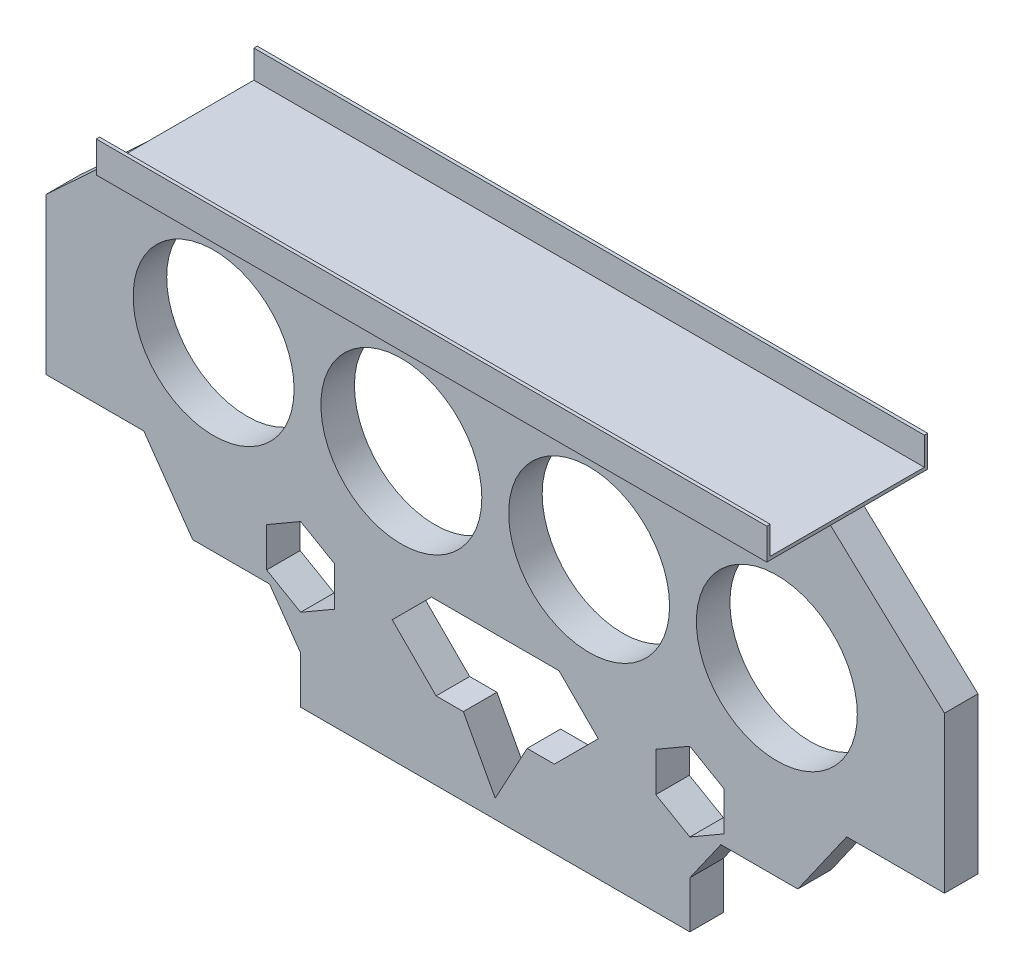
SolidWorks part; units mm, degrees
ref_plane "Front Plane" through (0, 0, 0) normal (0, 0, 1) x (1, 0, 0)
ref_plane "Top Plane" through (0, 0, 0) normal (0, 1, 0) x (1, 0, 0)
ref_plane "Right Plane" through (0, 0, 0) normal (1, 0, 0) x (0, 0, -1)
sketch "Sketch1" plane through (0, 0, 0) normal (0, 0, 1) x (1, 0, 0)
  line L1 (-67, -31.5) -> (67, -31.5)
  line L2 (-67, -31.5) -> (-67, 31.5)
  line L3 (-67, 31.5) -> (67, 31.5)
  line L4 (67, -31.5) -> (67, 31.5)
  line L5 (-67, -31.5) -> (67, 31.5) construction
  line L6 (-67, 31.5) -> (67, -31.5) construction
  point P0 (0, 0)
  dimension "D1" = 134
  dimension "D2" = 63
extrude "Boss-Extrude1" add sketch "Sketch1" against normal blind 5
sketch "Sketch3" plane through (0, 0, 0) normal (0, 0, 1) x (1, 0, 0)
  line L0 (-67, 31.5) -> (-67, -31.5) construction
  line L2 (67, -31.5) -> (67, 31.5) construction
  circle A0 centre (-42, 9.0713) radius 12
  circle A1 centre (-14, 9.0713) radius 12
  circle A2 centre (14, 9.0713) radius 12
  circle A3 centre (42, 9.0713) radius 12
  dimension "D1" = 28
  dimension "D2" = 25
  dimension "D3" = 28
  dimension "D4" = 28
  dimension "D5" = 25
extrude "Cut-Extrude1" cut sketch "Sketch3" against normal blind 10 contours A1 | A0 | A2 | A3
sketch "Sketch4" plane through (0, 0, 0) normal (0, 0, 1) x (1, 0, 0)
  line L0 (-67, -7.5206) -> (-52.4118, -7.5206)
  line L1 (-67, 31.5) -> (-67, -31.5) construction
  line L2 (-52.4118, -7.5206) -> (-45.1238, -17.91)
  line L3 (-45.1238, -17.91) -> (-33.649, -17.91)
  line L4 (-33.649, -17.91) -> (-29.0235, -24.5037)
  line L5 (-29.0235, -24.5037) -> (-29.0235, -31.5)
  line L6 (-67, -31.5) -> (67, -31.5) construction
  line L7 (-67, -7.5206) -> (-67, -31.5)
  line L8 (-67, -31.5) -> (-29.0235, -31.5)
  line L9 (0, 43.4956) -> (0, -7.5206) construction
  line L10 (67, -7.5206) -> (67, -31.5)
  line L11 (67, -7.5206) -> (52.4118, -7.5206)
  line L12 (52.4118, -7.5206) -> (45.1238, -17.91)
  line L13 (45.1238, -17.91) -> (33.649, -17.91)
  line L14 (33.649, -17.91) -> (29.0235, -24.5037)
  line L15 (29.0235, -24.5037) -> (29.0235, -31.5)
  line L16 (67, -31.5) -> (29.0235, -31.5)
  line L17 (-50, 31.5) -> (-67, 15.739)
  line L18 (67, 31.5) -> (-67, 31.5) construction
  line L19 (-67, 15.739) -> (-67, 31.5)
  line L20 (-67, 31.5) -> (-50, 31.5)
  line L21 (67, 15.739) -> (67, 31.5)
  line L22 (50, 31.5) -> (67, 15.739)
  line L23 (67, 31.5) -> (50, 31.5)
  line L24 (9.5114, -7.5206) -> (-9.5114, -7.5206)
  line L25 (-9.5114, -7.5206) -> (-15.37, -13.3792)
  line L26 (-15.37, -13.3792) -> (-8.816, -19.9332)
  line L27 (-8.816, -19.9332) -> (-4.7557, -19.9332)
  line L28 (-4.7557, -19.9332) -> (-2.2907, -24.5037)
  line L29 (-2.2907, -24.5037) -> (0, -28.751)
  line L31 (2.2907, -24.5037) -> (0, -28.751)
  line L32 (4.7557, -19.9332) -> (2.2907, -24.5037)
  line L33 (8.816, -19.9332) -> (4.7557, -19.9332)
  line L34 (15.37, -13.3792) -> (8.816, -19.9332)
  line L35 (9.5114, -7.5206) -> (15.37, -13.3792)
  line L36 (0, -28.751) -> (0, -47.0621) construction
  line L37 (-34.0972, -10.4499) -> (-29.0235, -7.5206)
  line L38 (29.0235, -7.5206) -> (23.9498, -10.4499)
  line L39 (23.9498, -10.4499) -> (23.9498, -16.3085)
  line L40 (23.9498, -16.3085) -> (29.0235, -19.2378)
  line L41 (29.0235, -19.2378) -> (34.0972, -16.3085)
  line L42 (34.0972, -16.3085) -> (34.0972, -10.4499)
  line L43 (34.0972, -10.4499) -> (29.0235, -7.5206)
  line L44 (-34.0972, -16.3085) -> (-34.0972, -10.4499)
  line L45 (-29.0235, -19.2378) -> (-34.0972, -16.3085)
  line L46 (-23.9498, -16.3085) -> (-29.0235, -19.2378)
  line L47 (-23.9498, -10.4499) -> (-23.9498, -16.3085)
  line L48 (-29.0235, -7.5206) -> (-23.9498, -10.4499)
  circle A0 centre (29.0235, -13.3792) radius 5.0737 construction
  dimension "D1" = 100
extrude "Cut-Extrude2" cut sketch "Sketch4" against normal blind 10
ref_plane "Plane1" through (50, 0, 0) normal (1, 0, 0) x (0, 0, -1)
sketch "Sketch5" plane through (50, 0, 0) normal (1, 0, 0) x (0, 0, -1)
  line L6 (2.5, 31.5) -> (2.5, 47.421) construction
  line L7 (5, 31.5) -> (0, 31.5) construction
  line L16 (-9.5, 31.5) -> (14.5, 31.5)
  line L17 (-9.5, 31.5) -> (-9.5, 36.1491)
  line L18 (-9.5, 36.1491) -> (-9, 36.1491)
  line L19 (-9, 36.1491) -> (-9, 32)
  line L20 (-9, 32) -> (14, 32)
  line L21 (14, 32) -> (14, 36.1491)
  line L22 (14, 36.1491) -> (14.5, 36.1491)
  line L23 (14.5, 36.1491) -> (14.5, 31.5)
  point P0 (2.5, 31.5)
  point P3 (2.5, 31.5)
  dimension "D1" = 24
  dimension "D2" = 0.5
  dimension "D3" = 0.5
  dimension "D4" = 0.5
extrude "Boss-Extrude2" add sketch "Sketch5" against normal blind 100
